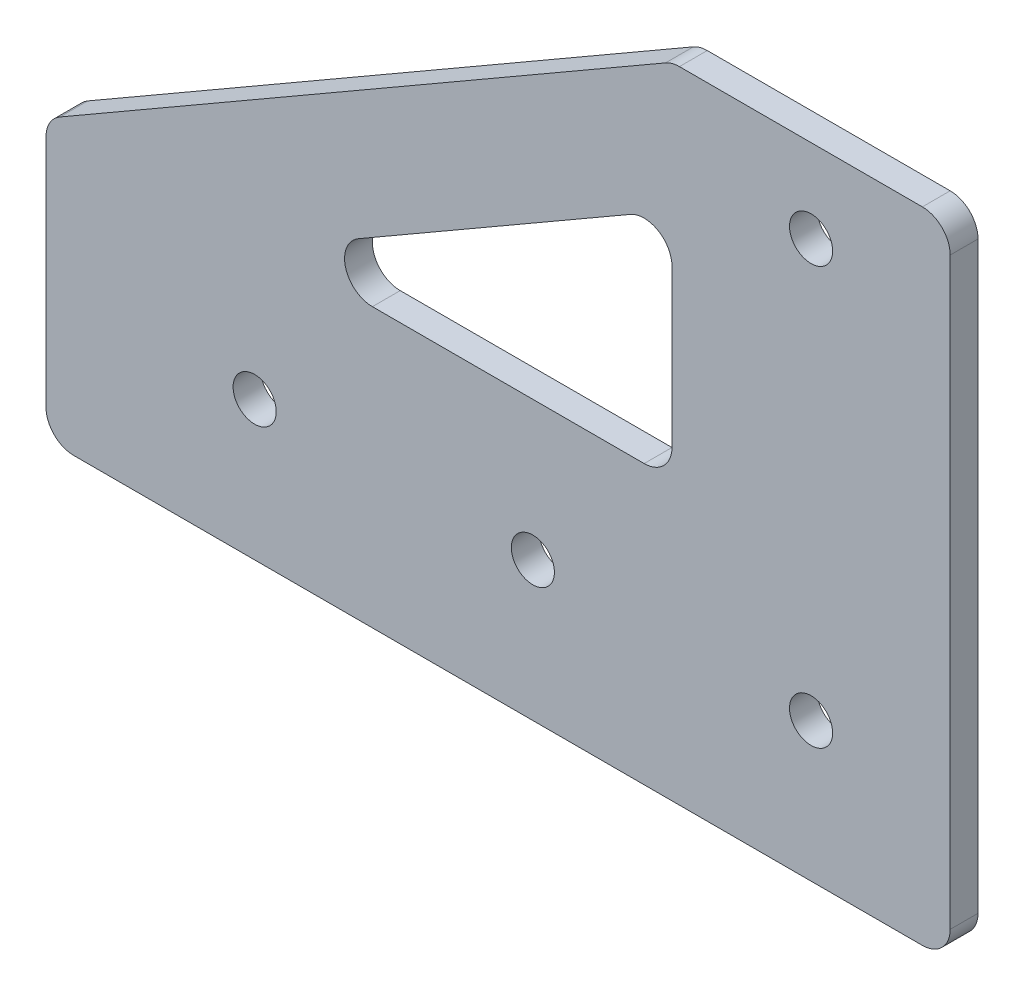
SolidWorks part; units mm, degrees
material "Thornel Mat VMA"
ref_plane "前视基准面" through (0, 0, 0) normal (0, 0, 1) x (1, 0, 0)
ref_plane "上视基准面" through (0, 0, 0) normal (0, 1, 0) x (1, 0, 0)
ref_plane "右视基准面" through (0, 0, 0) normal (1, 0, 0) x (0, 0, -1)
sketch "草图1" plane through (0, 0, 0) normal (0, 0, 1) x (1, 0, 0)
  line L0 (-55, -180) -> (10, -180)
  line L2 (10, -180) -> (10, -134.0192)
  line L3 (10, -160) -> (10, 0) construction
  line L4 (10, -134.0192) -> (-10, -134.0192)
  line L5 (-10, -160) -> (-10, 0) construction
  line L6 (-10, -134.0192) -> (-55, -160)
  line L8 (-55, -160) -> (-55, -180)
  line L9 (-54, -159.4226) -> (-11, -134.5966) construction
extrude "凸台-拉伸1" add sketch "草图1" along normal blind 2
sketch "草图2" plane through (0, 0, 0) normal (0, 0, -1) x (-1, 0, 0)
  line L0 (12, -160) -> (31.5359, -160) construction
  line L1 (32.5359, -156.2679) -> (13, -144.9889) construction
  line L2 (10, -146.7209) -> (10, -158) construction
  line L3 (12, -160) -> (31.5359, -160)
  line L4 (32.5359, -156.2679) -> (13, -144.9889)
  line L5 (10, -146.7209) -> (10, -158)
  arc A0 (31.5359, -160) -> (32.5359, -156.2679) centre (31.5359, -158) ccw construction
  arc A1 (13, -144.9889) -> (10, -146.7209) centre (12, -146.7209) ccw construction
  circle A2 centre (40, -170) radius 1.55 construction
  circle A3 centre (20, -170) radius 1.55 construction
  circle A4 centre (0, -170) radius 1.55 construction
  circle A5 centre (0, -140) radius 1.55 construction
  arc A6 (31.5359, -160) -> (32.5359, -156.2679) centre (31.5359, -158) ccw
  arc A7 (13, -144.9889) -> (10, -146.7209) centre (12, -146.7209) ccw
  circle A8 centre (40, -170) radius 1.55
  circle A9 centre (20, -170) radius 1.55
  circle A10 centre (0, -170) radius 1.55
  circle A11 centre (0, -140) radius 1.55
  arc A12 (10, -158) -> (12, -160) centre (12, -158) ccw construction
  arc A13 (10, -158) -> (12, -160) centre (12, -158) ccw
extrude "切除-拉伸1" cut sketch "草图2" against normal through all
fillet "圆角1" radius 2 5 edges at (-55, -160, 1) (10, -180, 1) (-55, -180, 1) (-10, -134.0192, 1) (10, -134.0192, 1)
